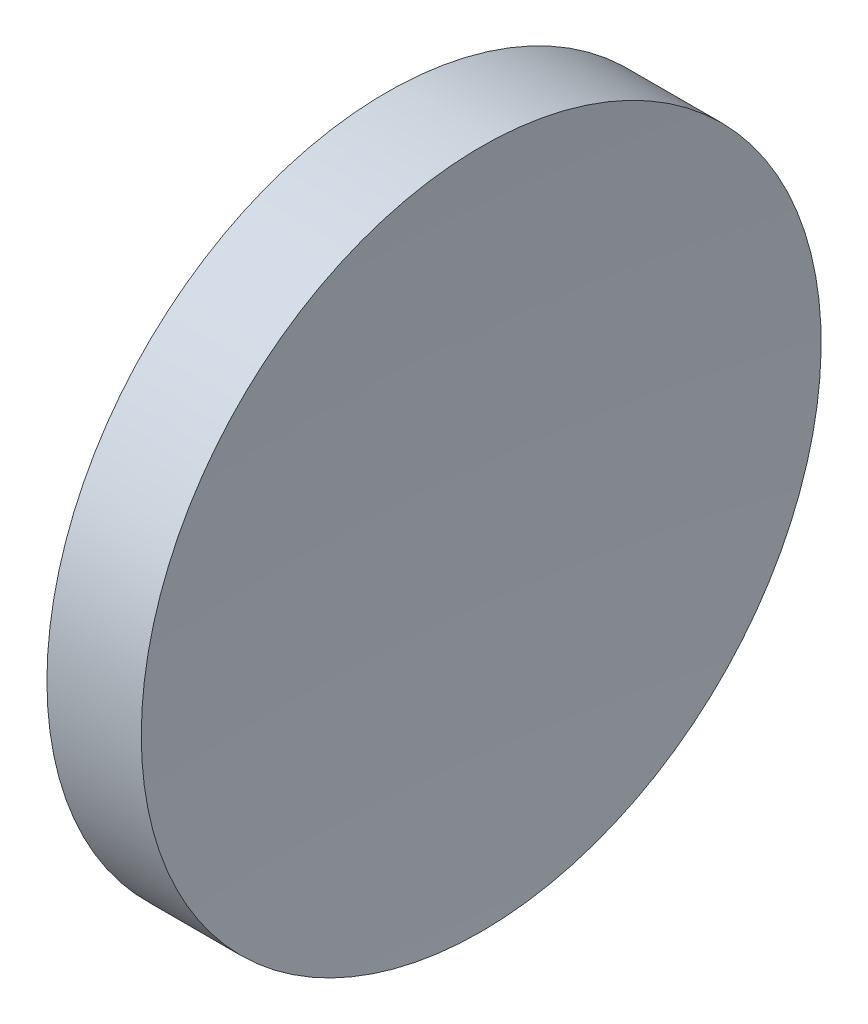
SolidWorks part; units mm, degrees
ref_plane "前视基准面" through (0, 0, 0) normal (0, 0, 1) x (1, 0, 0)
ref_plane "上视基准面" through (0, 0, 0) normal (0, 1, 0) x (1, 0, 0)
ref_plane "右视基准面" through (0, 0, 0) normal (1, 0, 0) x (0, 0, -1)
sketch "草图1" plane through (0, 0, 0) normal (0, 0, 1) x (1, 0, 0)
  line L0 (217.9703, 138.756) -> (265.5527, 138.756) construction
  line L1 (230.1996, 138.756) -> (230.1996, 176.256)
  line L2 (230.1996, 176.256) -> (240.6078, 176.256)
  line L3 (239.1996, 138.756) -> (230.1996, 138.756)
  arc A0 (240.6078, 176.256) -> (239.1996, 138.756) centre (739.1996, 138.756) ccw
  dimension "D1" = 500
revolve "旋转1" add sketch "草图1" angle 360 about L0
